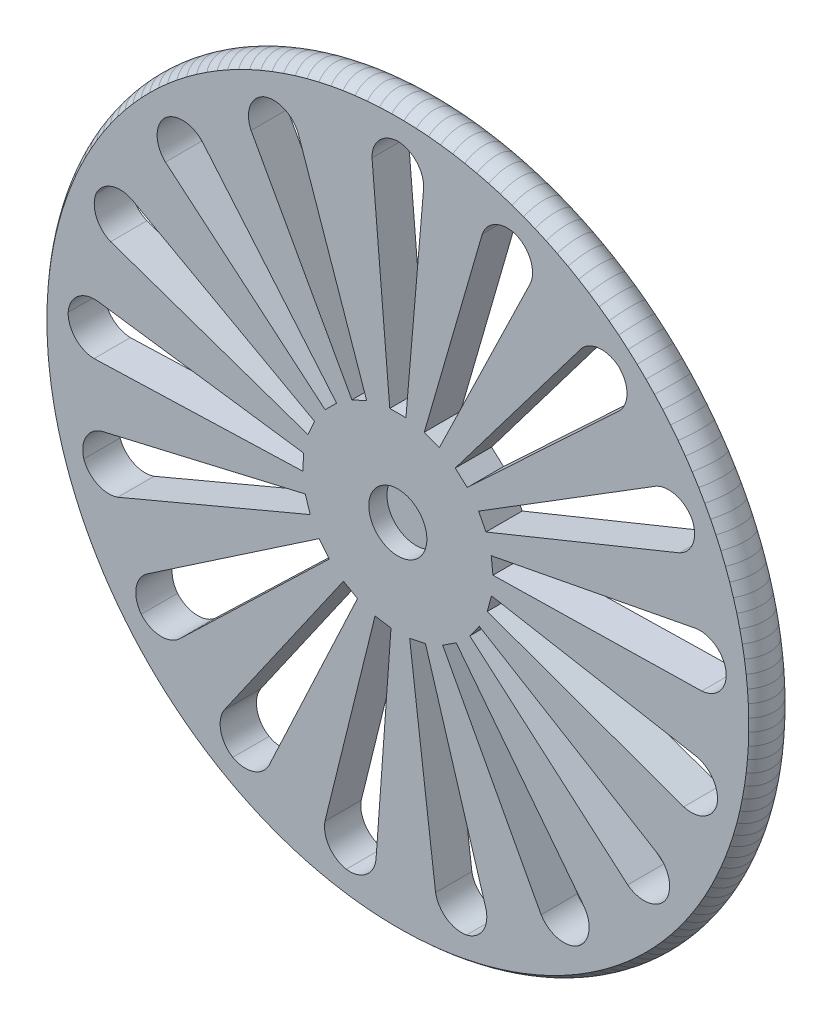
SolidWorks part; units mm, degrees
ref_plane "Front Plane" through (0, 0, 0) normal (0, 0, 1) x (1, 0, 0)
ref_plane "Top Plane" through (0, 0, 0) normal (0, 1, 0) x (1, 0, 0)
ref_plane "Right Plane" through (0, 0, 0) normal (1, 0, 0) x (0, 0, -1)
sketch "Sketch3" plane through (0, 0, 0) normal (0, 0, 1) x (1, 0, 0)
  circle A0 centre (0, 0) radius 48.025
  dimension "D1" = 96.05
extrude "Boss-Extrude2" add sketch "Sketch3" along normal mid plane 5
sketch "Sketch4" plane through (0, 0, 0) normal (0, 0, 1) x (1, 0, 0)
  line L0 (0, 0) -> (0, 45.4686) construction
  line L5 (1.1127, 13.0491) -> (-1.1127, 13.0491)
  line L6 (1.1127, 13.0491) -> (3.5562, 41.7066)
  line L7 (-1.1127, 13.0491) -> (-3.5562, 41.7066)
  arc A0 (3.5562, 41.7066) -> (0, 45.4686) centre (-0.1029, 41.8095) ccw
  arc A1 (-3.5562, 41.7066) -> (0, 45.4686) centre (0.1029, 41.8095) cw
  point P10 (0, 17.6588)
  point P11 (0, 13.0491)
extrude "Cut-Extrude1" cut sketch "Sketch4" along normal mid plane 5
pattern_circular "CirPattern2" count 17 every 21 about axis through (0, 0, 0) along (0, 0, 1) of "Cut-Extrude1"
sketch "Sketch6" plane through (0, 0, 0) normal (0, 0, 1) x (1, 0, 0)
  circle A0 centre (0, 0) radius 52.0211
  circle A1 centre (0, 0) radius 47.5
extrude "Boss-Extrude3" add sketch "Sketch6" along normal mid plane 5
sketch "Sketch8" plane through (0, 0, 0) normal (0, 1, 0) x (1, 0, 0)
  line L0 (52.0211, 2.5) -> (-52.0211, 2.5) construction
  line L1 (-52.0211, -2.5) -> (52.0211, -2.5) construction
  line L2 (-48.3211, 2.5) -> (-52.0211, 2.5)
  line L3 (-52.0211, 2.5) -> (-52.0211, -2.5)
  line L4 (-52.0211, -2.5) -> (-48.3211, -2.5)
  arc A0 (-48.3211, 2.5) -> (-48.3211, -2.5) centre (-45.8716, 0) ccw
  dimension "D3" = 3.5
  dimension "D1" = 3.7
  dimension "D2" = 3.7
extrude "Cut-Extrude2" cut sketch "Sketch8" along normal mid plane 2
pattern_circular "CirPattern3" count 180 every 2 about axis through (0, 0, 2.5) along (0, 0, -1) of "Cut-Extrude2"
sketch "Sketch10" plane through (0, 0, 0) normal (0, 0, 1) x (1, 0, 0)
  circle A0 centre (0, 0) radius 4
  dimension "D1" = 8
extrude "Cut-Extrude3" cut sketch "Sketch10" along normal blind 3
